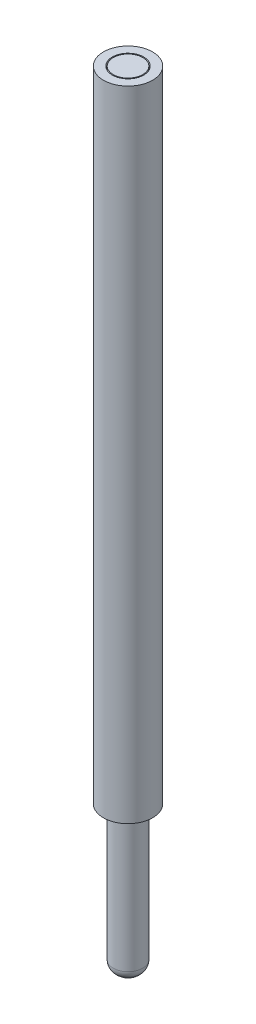
SolidWorks part; units mm, degrees
material "Brass"
ref_plane "Front plane" through (0, 0, 0) normal (0, 0, 1) x (1, 0, 0)
ref_plane "Top plane" through (0, 0, 0) normal (0, 1, 0) x (1, 0, 0)
ref_plane "Right Plane" through (0, 0, 0) normal (1, 0, 0) x (0, 0, -1)
sketch "Sketch1" plane through (0, 0, 0) normal (0, 0, 1) x (1, 0, 0)
  line L0 (0, 0) -> (0, 40)
  line L1 (0, 40) -> (0.75, 40)
  line L4 (0.75, 40) -> (0.75, 0.5)
  line L6 (0.8, 40) -> (1.25, 40)
  line L7 (0.8, 40) -> (0.8, 7.5)
  line L8 (0.8, 7.5) -> (1.25, 7.5)
  line L9 (1.25, 40) -> (1.25, 7.5)
  arc A0 (0, 0) -> (0.75, 0.5) centre (0, 0.8125) ccw
  dimension "D1" = 0.75
  dimension "D2" = 0.5
  dimension "D4" = 0.8
  dimension "D5" = 1.25
  dimension "D6" = 7.5
  dimension "D3" = 32.5
revolve "Revolve1" add sketch "Sketch1" angle 360 about L0
fillet "Fillet1" radius 0.5 1 edges at (0, 0.5, -0.75)
equation "\"l\"= 32.5"
equation "\"D3@Sketch1\"=\"l\""
